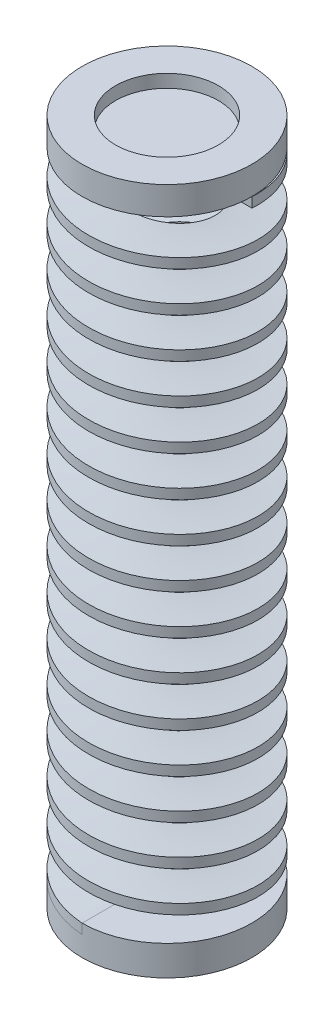
SolidWorks part; units mm, degrees
ref_plane "Front Plane" through (0, 0, 0) normal (0, 0, 1) x (1, 0, 0)
ref_plane "Top Plane" through (0, 0, 0) normal (0, 1, 0) x (1, 0, 0)
ref_plane "Right Plane" through (0, 0, 0) normal (1, 0, 0) x (0, 0, -1)
sketch "Sketch1" plane through (0, 0, 0) normal (0, 1, 0) x (1, 0, 0)
  circle A0 centre (0, 0) radius 7.5
curve "Helix/Spiral1" pitch 4 height 63 turns 15.75
sketch "Sketch4" plane through (0, 0, 0) normal (0, 0, 1) x (1, 0, 0)
  line L1 (-8.5, 1) -> (-4.25, 1)
  line L2 (-8.5, 1) -> (-8.5, 0)
  line L3 (-8.5, 0) -> (-4.25, 0)
  line L4 (-4.25, 1) -> (-4.25, 0)
  line L5 (-8.5, 1) -> (-4.25, 0) construction
  line L6 (-8.5, 0) -> (-4.25, 1) construction
  point P0 (-5.4233, 0.2761)
  dimension "D1" = 1
  dimension "D2" = 4.25
sweep "Sweep1" add profiles "Sketch4" path "Helix/Spiral1"
sketch "Sketch5" plane through (0, 0, 0) normal (0, 1, 0) x (1, 0, 0)
  circle A0 centre (0, 0) radius 8.5
extrude "Boss-Extrude1" add sketch "Sketch5" against normal blind 2
sketch3d "3DSketch1" plane through (0, 0, 0) normal (0, 0, 1) x (1, 0, 0)
  dimension "D1" = 90
sketch3d "3DSketch2"
  line L0 (8.5, 63, 0) -> (4.25, 63, 0) construction
sketch "Sketch6" plane through (0, -2, 0) normal (0, -1, 0) x (1, 0, 0)
  circle A0 centre (0, 0) radius 8.5
  circle A1 centre (0, 0) radius 5.15
extrude "Boss-Extrude2" add sketch "Sketch6" along normal blind 1
sketch3d "3DSketch8"
  line L0 (8.5, 63, 0) -> (4.25, 63, 0) construction
  point P6 (6.5779, 63, -5.277)
sketch "Sketch9" plane through (0, 63, 0) normal (0, 1, 0) x (1, 0, 0)
  circle A0 centre (0, 0) radius 8.5
extrude "Boss-Extrude5" add sketch "Sketch9" along normal blind 1.5 separate body
sketch "Sketch10" plane through (0, 64.5, 0) normal (0, 1, 0) x (1, 0, 0)
  circle A0 centre (0, 0) radius 8.5
  circle A1 centre (0, 0) radius 5.15
extrude "Boss-Extrude6" add sketch "Sketch10" along normal blind 1.3
